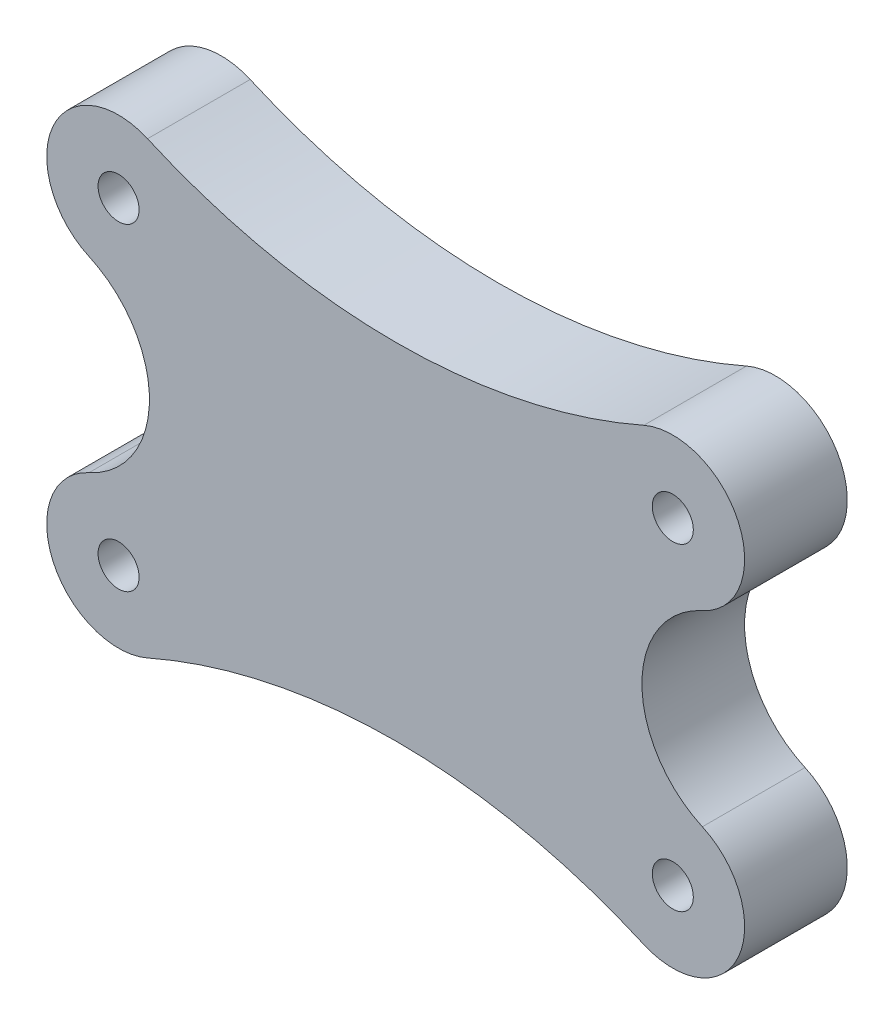
SolidWorks part; units mm, degrees
ref_plane "Plan de face" through (0, 0, 0) normal (0, 0, 1) x (1, 0, 0)
ref_plane "Plan de dessus" through (0, 0, 0) normal (0, 1, 0) x (1, 0, 0)
ref_plane "Plan de droite" through (0, 0, 0) normal (1, 0, 0) x (0, 0, -1)
sketch "Esquisse1" plane through (0, 0, 0) normal (0, 0, 1) x (1, 0, 0)
  line L0 (-17, -0.1216) -> (-17, -8.3527) construction
  line L4 (0, 0) -> (-34, 0)
  line L5 (0, 0) -> (0, 22.5)
  line L6 (0, 22.5) -> (-34, 22.5)
  line L7 (-34, 0) -> (-34, 22.5)
  line L30 (0, 13.35) -> (0, 9.15)
  line L31 (-34, 13.35) -> (-34, 9.15)
  line L34 (-34, 18.75) -> (-34, 3.75)
  line L39 (0, 18.75) -> (0, 3.75)
  line L43 (0, 11.25) -> (25.2759, 11.25) construction
  circle A6 centre (-30.5, 19) radius 1
  circle A7 centre (-3.5, 19) radius 1
  circle A8 centre (-3.5, 3.5) radius 1
  circle A10 centre (-30.5, 3.5) radius 1
  dimension "D7" = 13.5
  dimension "D9" = 3.5
  dimension "D10" = 2
  dimension "D11" = 2
  dimension "D3" = 13.5
  dimension "D4" = 22.5
  dimension "D2" = 34
  dimension "D15" = 13.5
extrude "Boss.-Extru.1" add sketch "Esquisse1" along normal blind 5
sketch "Sketch1" plane through (0, 0, 0) normal (0, 0, -1) x (-1, 0, 0)
  line L0 (34, 11.25) -> (28.9963, 11.25) construction
  line L1 (34, 0) -> (34, 22.5) construction
  line L2 (0, 0) -> (0, 22.5) construction
  line L3 (17, 22.5) -> (17, 19.6594) construction
  line L4 (0, 22.5) -> (34, 22.5) construction
  line L5 (0, 0) -> (34, 0) construction
  line L6 (5.0037, 11.25) -> (0, 11.25) construction
  line L7 (17, 2.8406) -> (17, 0) construction
  line L8 (35.959, 25.0367) -> (37.5255, -3.2855)
  line L9 (35.959, 25.0367) -> (-8.0268, 22.604)
  line L10 (37.5255, -3.2855) -> (-6.4603, -5.7183)
  line L11 (-8.0268, 22.604) -> (-6.4603, -5.7183)
  arc A0 (31.9406, 15.8102) -> (29.0896, 22.2032) centre (30.5, 19) ccw
  arc A1 (29.0896, 0.2968) -> (31.9406, 6.6898) centre (30.5, 3.5) ccw
  arc A2 (2.0594, 6.6898) -> (4.9104, 0.2968) centre (3.5, 3.5) ccw
  arc A3 (4.9104, 22.2032) -> (2.0594, 15.8102) centre (3.5, 19) ccw
  arc A4 (31.9406, 15.8102) -> (31.9406, 6.6898) centre (34, 11.25) ccw
  arc A5 (2.0594, 6.6898) -> (2.0594, 15.8102) centre (0, 11.25) ccw
  arc A6 (29.0896, 0.2968) -> (4.9104, 0.2968) centre (17, -27.1594) ccw
  arc A8 (29.0896, 22.2032) -> (4.9104, 22.2032) centre (17, 49.6594) cw
  dimension "D1" = 60
extrude "Cut-Extrude1" cut sketch "Sketch1" against normal blind 10
